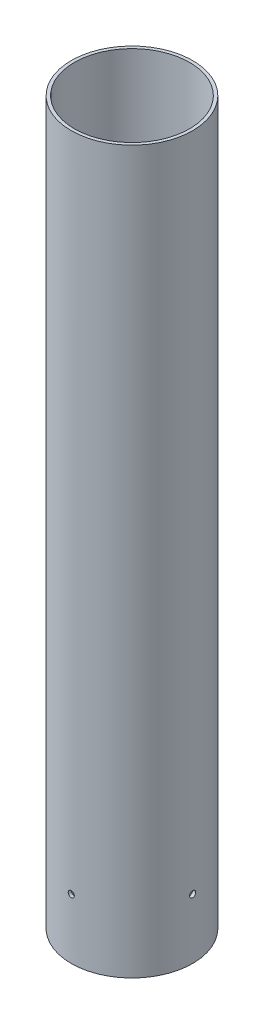
SolidWorks part; units mm, degrees
ref_plane "Front Plane" through (0, 0, 0) normal (0, 0, 1) x (1, 0, 0)
ref_plane "Top Plane" through (0, 0, 0) normal (0, 1, 0) x (1, 0, 0)
ref_plane "Right Plane" through (0, 0, 0) normal (1, 0, 0) x (0, 0, -1)
sketch "Sketch1" plane through (0, 0, 0) normal (0, 1, 0) x (1, 0, 0)
  circle A0 centre (0, 0) radius 36.5
  circle A1 centre (0, 0) radius 38.5
  dimension "D1" = 77
  dimension "D2" = 2
extrude "Boss-Extrude1" add sketch "Sketch1" along normal blind 457.2
sketch "Sketch2" plane through (0, 0, 0) normal (1, 0, 0) x (0, 0, -1)
  line L0 (0, 0) -> (0, 38.1) construction
  circle A0 centre (0, 38.1) radius 1.95
  dimension "D1" = 3.9
  dimension "D2" = 38.1
extrude "Cut-Extrude1" cut sketch "Sketch2" against normal through all both and the other way through all
sketch "Sketch3" plane through (0, 0, 0) normal (0, 0, 1) x (1, 0, 0)
  line L0 (0, 0) -> (0, 38.1) construction
  circle A0 centre (0, 38.1) radius 1.95
  dimension "D1" = 3.9
  dimension "D2" = 38.1
extrude "Cut-Extrude2" cut sketch "Sketch3" against normal through all both and the other way through all
